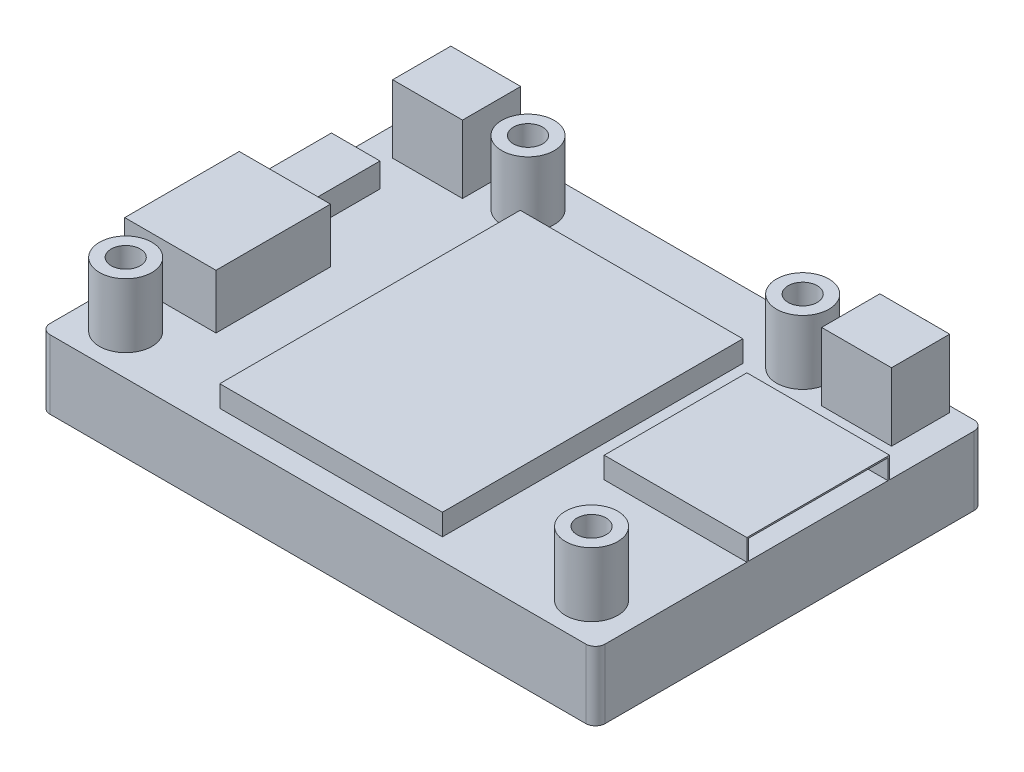
SolidWorks part; units mm, degrees
ref_plane "Plano frontal" through (0, 0, 0) normal (0, 0, 1) x (1, 0, 0)
ref_plane "Plano superior" through (0, 0, 0) normal (0, 1, 0) x (1, 0, 0)
ref_plane "Plano direito" through (0, 0, 0) normal (1, 0, 0) x (0, 0, -1)
sketch "Esboço1" plane through (0, 0, 0) normal (0, 1, 0) x (1, 0, 0)
  line L1 (0, 0) -> (57.2, 0)
  line L2 (0, 0) -> (0, 40)
  line L3 (0, 40) -> (57.2, 40)
  line L4 (57.2, 0) -> (57.2, 40)
  dimension "D1" = 57.2
  dimension "D2" = 40
extrude "Ressalto-extrusão1" add sketch "Esboço1" along normal blind 7.1
sketch "Esboço2" plane through (0, 7.1, 0) normal (0, 1, 0) x (1, 0, 0)
  line L0 (14.45, 35.8) -> (42.75, 35.8) construction
  line L1 (42.75, 35.8) -> (52.6, 4.2) construction
  line L2 (52.6, 4.2) -> (4.6, 4.2) construction
  line L3 (4.6, 4.2) -> (14.45, 35.8) construction
  line L4 (28.6, 35.8) -> (28.6, 4.2) construction
  line L5 (28.6, 20) -> (57.2, 20) construction
  line L6 (57.2, 0) -> (57.2, 40) construction
  line L7 (57.2, 20) -> (28.6, 40) construction
  line L8 (57.2, 40) -> (0, 40) construction
  line L9 (28.6, 40) -> (28.6, 35.8) construction
  line L10 (0, 0) -> (57.2, 0) construction
  circle A0 centre (4.6, 4.2) radius 2.7
  circle A1 centre (52.6, 4.2) radius 2.7
  circle A2 centre (42.75, 35.8) radius 2.7
  circle A3 centre (14.45, 35.8) radius 2.7
  point P14 (55.3, 4.2)
  point P18 (1.9, 4.2)
  point P19 (40.05, 35.8)
  point P20 (14.45, 38.5)
  point P21 (17.15, 35.8)
  point P22 (42.75, 38.5)
  point P23 (4.6, 1.5)
  point P24 (52.6, 1.5)
  dimension "D1" = 5.4
  dimension "D2" = 53.4
  dimension "D3" = 22.9
  dimension "D4" = 1.5
extrude "Ressalto-extrusão2" add sketch "Esboço2" along normal blind 6.6
sketch "Esboço3" plane through (0, 13.7, 0) normal (0, 1, 0) x (1, 0, 0)
  circle A0 centre (14.45, 35.8) radius 1.5
  circle A1 centre (42.75, 35.8) radius 1.5
  circle A2 centre (52.6, 4.2) radius 1.5
  circle A3 centre (4.6, 4.2) radius 1.5
  dimension "D1" = 3
extrude "Corte-extrusão1" cut sketch "Esboço3" against normal up to surface (6.6 mm away) up to face at (14.45, 7.1, -38.5)
sketch "Esboço4" plane through (0, 0, 0) normal (0, -1, 0) x (-1, 0, 0)
  line L1 (-3.426, 3.3335) -> (-44.076, 3.3335)
  line L2 (-3.426, 3.3335) -> (-3.426, 37.0149)
  line L3 (-3.426, 37.0149) -> (-44.076, 37.0149)
  line L4 (-44.076, 3.3335) -> (-44.076, 37.0149)
extrude "Corte-extrusão2" cut sketch "Esboço4" against normal blind 0.1
sketch "Esboço5" plane through (0, 7.1, 0) normal (0, 1, 0) x (1, 0, 0)
  line L0 (57.2, 0) -> (57.2, 40) construction
  line L1 (57.2, 30.3) -> (42.5, 30.3)
  line L2 (57.2, 30.3) -> (57.2, 15.6)
  line L3 (57.2, 15.6) -> (42.5, 15.6)
  line L4 (42.5, 30.3) -> (42.5, 15.6)
  line L5 (57.2, 40) -> (0, 40) construction
  dimension "D1" = 24.4
  dimension "D2" = 14.7
  dimension "D3" = 14.7
extrude "Ressalto-extrusão3" add sketch "Esboço5" along normal blind 2.2
sketch "Esboço6" plane through (57.2, 0, 0) normal (1, 0, 0) x (0, 0, -1)
  line L1 (15.7661, 9.1497) -> (30.1347, 9.1497)
  line L2 (15.7661, 9.1497) -> (15.7661, 7.1073)
  line L3 (15.7661, 7.1073) -> (30.1347, 7.1073)
  line L4 (30.1347, 9.1497) -> (30.1347, 7.1073)
extrude "Corte-extrusão3" cut sketch "Esboço6" against normal blind 10
sketch "Esboço7" plane through (0, 7.1, 0) normal (0, 1, 0) x (1, 0, 0)
  line L0 (0, 40) -> (0, 0) construction
  line L1 (0, 8.7) -> (9.4, 8.7)
  line L2 (0, 8.7) -> (0, 20.5)
  line L3 (0, 20.5) -> (9.4, 20.5)
  line L4 (9.4, 8.7) -> (9.4, 20.5)
  line L5 (57.2, 40) -> (0, 40) construction
  line L6 (0, 22.7) -> (5, 22.7)
  line L7 (0, 22.7) -> (0, 30)
  line L8 (0, 30) -> (5, 30)
  line L9 (5, 22.7) -> (5, 30)
  line L10 (0, 0) -> (57.2, 0) construction
  dimension "D1" = 11.8
  dimension "D2" = 7.3
  dimension "D3" = 17.3
  dimension "D4" = 20.5
  dimension "D5" = 5
  dimension "D6" = 9.4
extrude "Ressalto-extrusão4" add sketch "Esboço7" along normal blind 2.5
sketch "Esboço8" plane through (0, 9.6, 0) normal (0, 1, 0) x (1, 0, 0)
  line L1 (9.4, 20.5) -> (0, 20.5)
  line L2 (9.4, 20.5) -> (9.4, 8.7)
  line L3 (9.4, 8.7) -> (0, 8.7)
  line L4 (0, 20.5) -> (0, 8.7)
extrude "Ressalto-extrusão5" add sketch "Esboço8" along normal blind 3.1
sketch "Esboço9" plane through (0, 0, 0) normal (-1, 0, 0) x (0, 0, 1)
  line L1 (-28.9544, 9.0835) -> (-23.1878, 9.0835)
  line L2 (-28.9544, 9.0835) -> (-28.9544, 7.2155)
  line L3 (-28.9544, 7.2155) -> (-23.1878, 7.2155)
  line L4 (-23.1878, 9.0835) -> (-23.1878, 7.2155)
  line L5 (-19.6142, 12.0074) -> (-9.2182, 12.0074)
  line L6 (-19.6142, 12.0074) -> (-19.6142, 7.2155)
  line L7 (-19.6142, 7.2155) -> (-9.2182, 7.2155)
  line L8 (-9.2182, 12.0074) -> (-9.2182, 7.2155)
  line L9 (-18.3553, 10.6267) -> (-16.6091, 10.6267)
  line L10 (-18.3553, 10.6267) -> (-18.3553, 8.5962)
  line L11 (-18.3553, 8.5962) -> (-16.6091, 8.5962)
  line L12 (-16.6091, 10.6267) -> (-16.6091, 8.5962)
  line L13 (-15.2284, 10.6267) -> (-14.1319, 10.6267)
  line L14 (-15.2284, 10.6267) -> (-15.2284, 8.5962)
  line L15 (-15.2284, 8.5962) -> (-14.1319, 8.5962)
  line L16 (-14.1319, 10.6267) -> (-14.1319, 8.5962)
  line L17 (-13.1979, 10.6267) -> (-11.9796, 10.6267)
  line L18 (-13.1979, 10.6267) -> (-13.1979, 8.5962)
  line L19 (-13.1979, 8.5962) -> (-11.9796, 8.5962)
  line L20 (-11.9796, 10.6267) -> (-11.9796, 8.5962)
  line L21 (-11.0456, 10.6267) -> (-10.2741, 10.6267)
  line L22 (-11.0456, 10.6267) -> (-11.0456, 8.5962)
  line L23 (-11.0456, 8.5962) -> (-10.2741, 8.5962)
  line L24 (-10.2741, 10.6267) -> (-10.2741, 8.5962)
extrude "Corte-extrusão4" cut sketch "Esboço9" against normal blind 3.1
fillet "Filete1" radius 1 4 edges at (57.2, 3.55, -40) (57.2, 3.55, 0) (0, 3.55, -40) (0, 3.55, 0)
sketch "Esboço10" plane through (0, 7.1, 0) normal (0, 1, 0) x (1, 0, 0)
  line L1 (16.3179, 33.1241) -> (39.2561, 33.1241)
  line L2 (16.3179, 33.1241) -> (16.3179, 2.1721)
  line L3 (16.3179, 2.1721) -> (39.2561, 2.1721)
  line L4 (39.2561, 33.1241) -> (39.2561, 2.1721)
extrude "Ressalto-extrusão6" add sketch "Esboço10" along normal blind 2.2 contours L2 L1 L4 L3
sketch "Esboço11" plane through (0, 7.1, 0) normal (0, 1, 0) x (1, 0, 0)
  line L0 (10.1, 39.4) -> (47.1, 39.4) construction
  line L1 (2.9, 39.4) -> (10.1, 39.4)
  line L2 (2.9, 39.4) -> (2.9, 33.4)
  line L3 (2.9, 33.4) -> (10.1, 33.4)
  line L4 (10.1, 39.4) -> (10.1, 33.4)
  line L5 (47.1, 39.4) -> (54.3, 39.4)
  line L6 (47.1, 39.4) -> (47.1, 33.4)
  line L7 (47.1, 33.4) -> (54.3, 33.4)
  line L8 (54.3, 39.4) -> (54.3, 33.4)
  line L9 (28.6, 39.4) -> (28.6, 40) construction
  line L10 (56.2, 40) -> (1, 40) construction
  dimension "D1" = 7.2
  dimension "D2" = 6
  dimension "D3" = 51.4
  dimension "D4" = 0.6
extrude "Ressalto-extrusão7" add sketch "Esboço11" along normal blind 7
sketch "Esboço12" plane through (0, 0, -39.4) normal (0, 0, -1) x (-1, 0, 0)
  circle A0 centre (-50.743, 10.7783) radius 2.1358
  circle A1 centre (-6.357, 10.7783) radius 1.9753
extrude "Ressalto-extrusão8" add sketch "Esboço12" along normal blind 1.2
